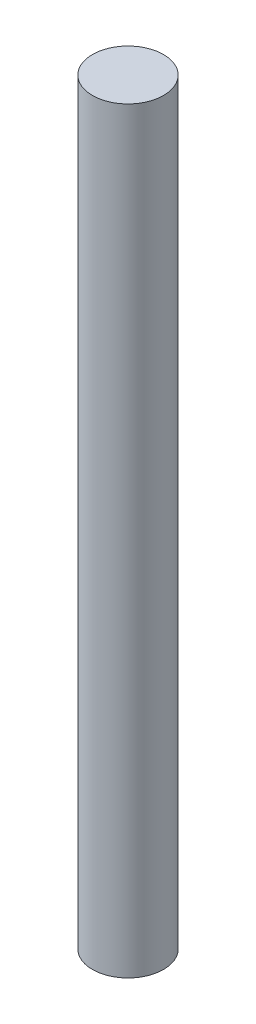
SolidWorks part; units mm, degrees
ref_plane "Front Plane" through (0, 0, 0) normal (0, 0, 1) x (1, 0, 0)
ref_plane "Top Plane" through (0, 0, 0) normal (0, 1, 0) x (1, 0, 0)
ref_plane "Right Plane" through (0, 0, 0) normal (1, 0, 0) x (0, 0, -1)
sketch "Sketch1" plane through (0, 0, 0) normal (0, 1, 0) x (1, 0, 0)
  circle A0 centre (0, 0) radius 4
  dimension "D1" = 8
extrude "Boss-Extrude1" add sketch "Sketch1" along normal blind 95
sketch "Sketch2" plane through (0, 95, 0) normal (0, 1, 0) x (1, 0, 0)
  circle A0 centre (0, 0) radius 4 construction
  circle A1 centre (0, 0) radius 4
extrude "Cut-Extrude1" cut sketch "Sketch2" against normal blind 9.74
